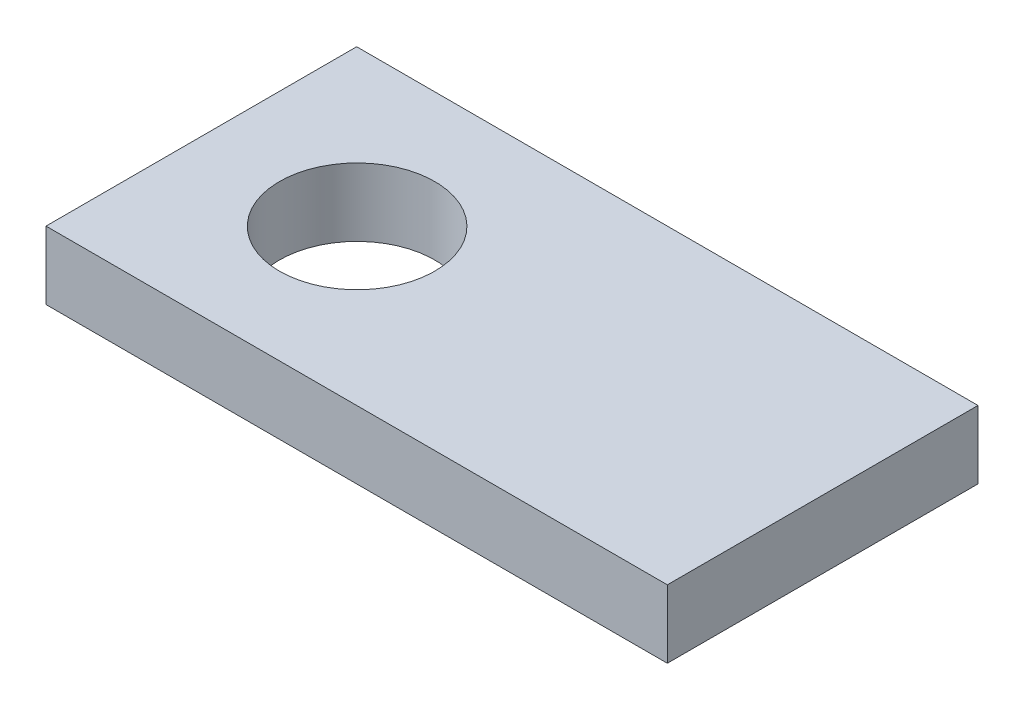
SolidWorks part; units mm, degrees
material "Pine"
ref_plane "Front Plane" through (0, 0, 0) normal (0, 0, 1) x (1, 0, 0)
ref_plane "Top Plane" through (0, 0, 0) normal (0, 1, 0) x (1, 0, 0)
ref_plane "Right Plane" through (0, 0, 0) normal (1, 0, 0) x (0, 0, -1)
sketch "Sketch1" plane through (0, 0, 0) normal (0, 1, 0) x (1, 0, 0)
  line L1 (-50.8, -25.4) -> (50.8, -25.4)
  line L2 (-50.8, -25.4) -> (-50.8, 25.4)
  line L3 (-50.8, 25.4) -> (50.8, 25.4)
  line L4 (50.8, -25.4) -> (50.8, 25.4)
  line L5 (-50.8, -25.4) -> (50.8, 25.4) construction
  line L6 (-50.8, 25.4) -> (50.8, -25.4) construction
  circle A0 centre (-25.3257, 0) radius 12.7
  point P0 (0, 0)
  dimension "D3" = 25.4
  dimension "D1" = 50.8
  dimension "D2" = 101.6
extrude "Boss-Extrude1" add sketch "Sketch1" along normal blind 11.1125
